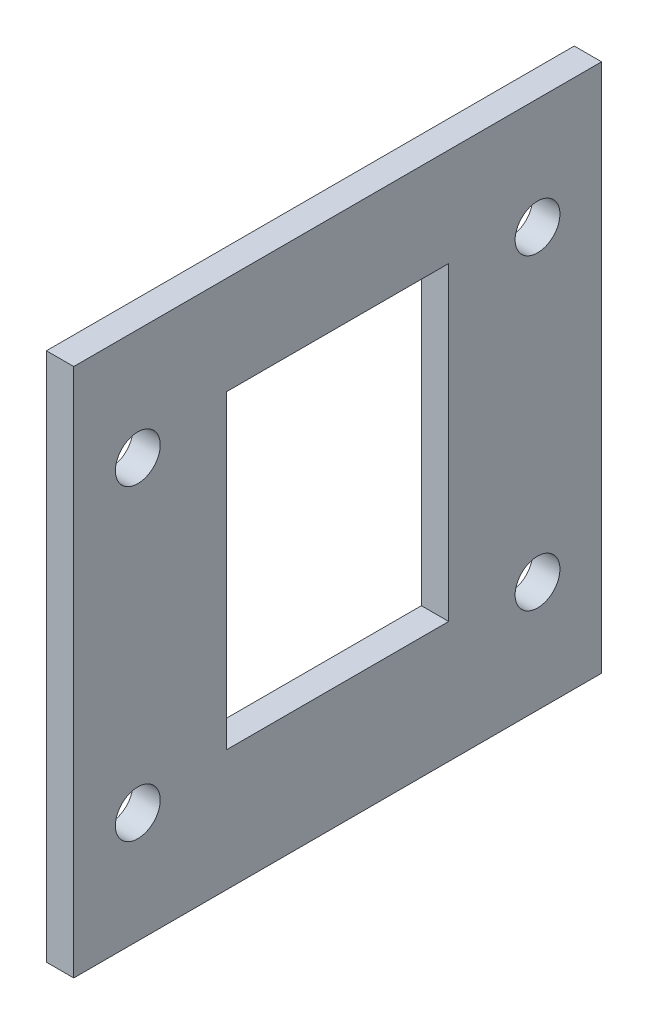
SolidWorks part; units mm, degrees
material "AISI 304"
ref_plane "Front Plane" through (0, 0, 0) normal (0, 0, 1) x (1, 0, 0)
ref_plane "Top Plane" through (0, 0, 0) normal (0, 1, 0) x (1, 0, 0)
ref_plane "Right Plane" through (0, 0, 0) normal (1, 0, 0) x (0, 0, -1)
sketch "Sketch1" plane through (0, 0, 0) normal (1, 0, 0) x (0, 0, -1)
  line L1 (0, 0) -> (61.8, 0)
  line L2 (0, 0) -> (0, 62)
  line L3 (0, 62) -> (61.8, 62)
  line L4 (61.8, 0) -> (61.8, 62)
  dimension "D1" = 61.8
  dimension "D2" = 62
extrude "Boss-Extrude1" add sketch "Sketch1" along normal blind 3.2
sketch "Sketch2" plane through (3.2, 0, 0) normal (1, 0, 0) x (0, 0, -1)
  line L0 (30.9, 62) -> (30.9, 0) construction
  line L1 (61.8, 62) -> (0, 62) construction
  line L2 (0, 0) -> (61.8, 0) construction
  line L4 (17.9, 14.2) -> (43.9, 14.2)
  line L5 (17.9, 14.2) -> (17.9, 50.5)
  line L7 (17.9, 50.5) -> (43.9, 50.5)
  line L8 (43.9, 14.2) -> (43.9, 50.5)
  line L9 (17.9, 14.2) -> (43.9, 50.5) construction
  line L10 (17.9, 50.5) -> (43.9, 14.2) construction
  point P6 (30.9, 32.35)
  point P13 (30.9, 0)
  dimension "D1" = 26
  dimension "D2" = 36.3
  dimension "D3" = 11.5
extrude "Cut-Extrude1" cut sketch "Sketch2" against normal up to next
sketch "Sketch3" plane through (0, 0, 0) normal (-1, 0, 0) x (0, 0, 1)
  circle A0 centre (-7.5, 49) radius 2.625
  circle A1 centre (-7.5, 13) radius 2.625
  circle A2 centre (-54.3, 49) radius 2.625
  circle A3 centre (-54.3, 13) radius 2.625
extrude "Cut-Extrude2" cut sketch "Sketch3" against normal up to next
